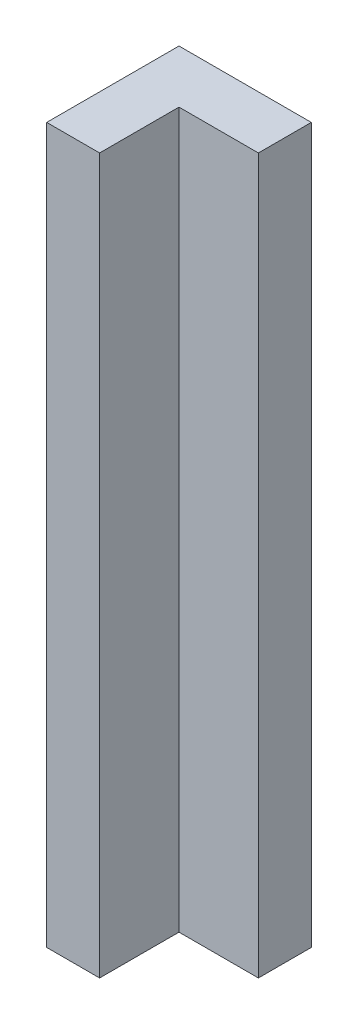
SolidWorks part; units mm, degrees
material "2014-T6"
ref_plane "Front Plane" through (0, 0, 0) normal (0, 0, 1) x (1, 0, 0)
ref_plane "Top Plane" through (0, 0, 0) normal (0, 1, 0) x (1, 0, 0)
ref_plane "Right Plane" through (0, 0, 0) normal (1, 0, 0) x (0, 0, -1)
sketch "Sketch1" plane through (0, 0, 0) normal (0, 1, 0) x (1, 0, 0)
  line L0 (-6.4324, 2.5) -> (-2.701, 2.5)
  line L1 (-2.701, 2.5) -> (-2.701, 0.5)
  line L2 (-2.701, 0.5) -> (-5.701, 0.5)
  line L3 (-5.701, 0.5) -> (-5.701, -2.5)
  line L4 (-5.701, -2.5) -> (-7.701, -2.5)
  line L5 (-7.701, -2.5) -> (-7.701, 2.5)
  line L6 (-7.701, 2.5) -> (-6.4324, 2.5)
  dimension "D1" = 2
  dimension "D2" = 5
  dimension "D3" = 5
extrude "Boss-Extrude1" add sketch "Sketch1" along normal blind 27
